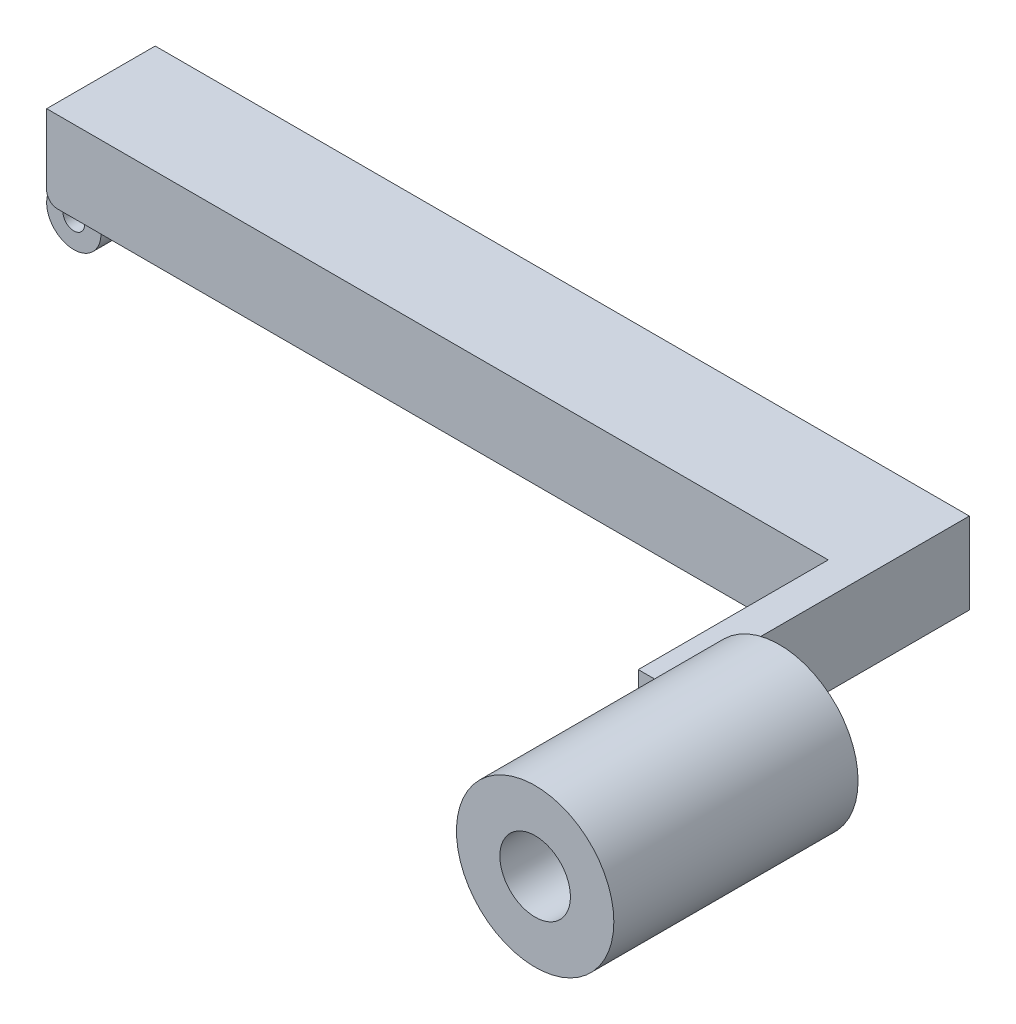
SolidWorks part; units mm, degrees
ref_plane "Front Plane" through (0, 0, 0) normal (0, 0, 1) x (1, 0, 0)
ref_plane "Top Plane" through (0, 0, 0) normal (0, 1, 0) x (1, 0, 0)
ref_plane "Right Plane" through (0, 0, 0) normal (1, 0, 0) x (0, 0, -1)
sketch "Sketch4" plane through (0, 0, 0) normal (1, 0, 0) x (0, 0, -1)
  line L1 (-10, -7.5) -> (10, -7.5)
  line L2 (-10, -7.5) -> (-10, 7.5)
  line L3 (-10, 7.5) -> (10, 7.5)
  line L4 (10, -7.5) -> (10, 7.5)
  line L5 (-10, -7.5) -> (10, 7.5) construction
  line L6 (-10, 7.5) -> (10, -7.5) construction
  point P0 (0, 0)
  dimension "D1" = 20
  dimension "D2" = 15
extrude "Boss-Extrude1" add sketch "Sketch4" along normal blind 150
sketch "Sketch5" plane through (0, 0, 10) normal (0, 0, 1) x (1, 0, 0)
  line L0 (150, -7.5) -> (0, -7.5) construction
  line L1 (150, 7.5) -> (144, 7.5)
  line L2 (150, 7.5) -> (150, -7.5)
  line L3 (150, -7.5) -> (144, -7.5)
  line L4 (144, 7.5) -> (144, -7.5)
  dimension "D1" = 6
extrude "Boss-Extrude2" add sketch "Sketch5" along normal blind 35
sketch "Sketch6" plane through (0, 0, 45) normal (0, 0, 1) x (1, 0, 0)
  line L0 (150, -7.5) -> (150, 7.5) construction
  circle A0 centre (160, 0) radius 6.5
  circle A1 centre (160, 0) radius 14.5
  point P6 (150, 0)
  dimension "D3" = 13
  dimension "D2" = 10
  dimension "D1" = 8
extrude "Boss-Extrude3" add sketch "Sketch6" against normal blind 10 and the other way blind 35
sketch "Sketch7" plane through (0, 0, 0) normal (0, 0, 1) x (1, 0, 0)
  line L0 (5, -12.5) -> (5, -7.5)
  line L1 (144, -7.5) -> (0, -7.5) construction
  line L2 (0, 7.5) -> (0, -7.5) construction
  line L3 (0, -7.5) -> (5, -7.5)
  circle A0 centre (0, -12.5) radius 2
  arc A2 (0, -7.5) -> (5, -12.5) centre (0, -12.5) ccw
  circle A3 centre (0, -12.5) radius 5 construction
  arc A4 (0, -7.5) -> (5, -12.5) centre (0, -12.5) cw construction
  dimension "D1" = 4
  dimension "D2" = 3
extrude "Boss-Extrude4" add sketch "Sketch7" along normal mid plane 10
fillet "Fillet1" radius 2 2 edges at (0, -7.5, -7.5) (0, -7.5, 7.5)
